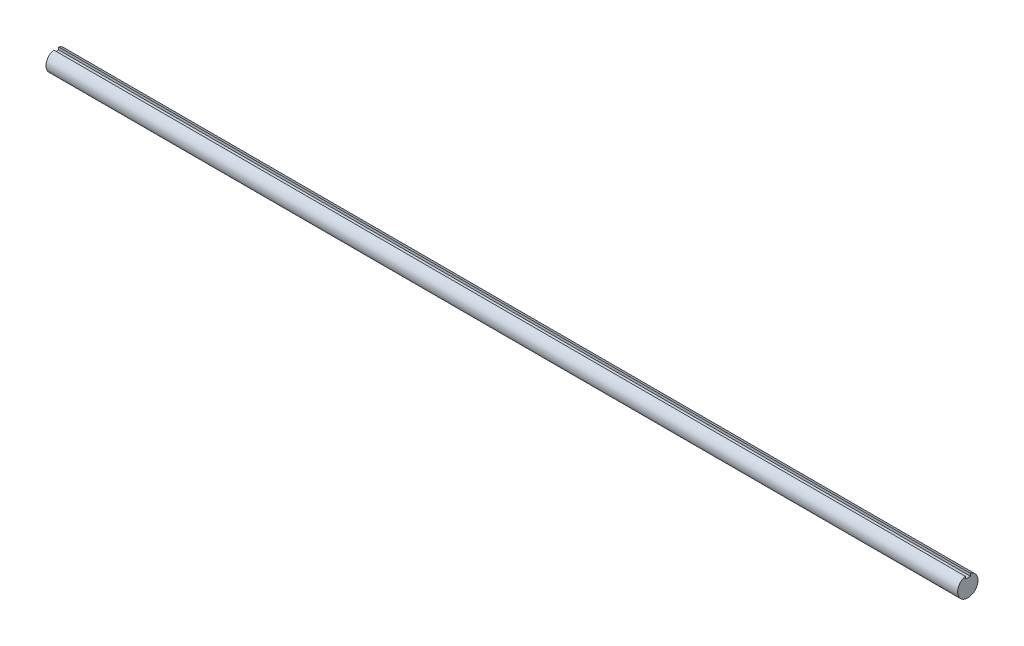
SolidWorks part; units mm, degrees
material "AISI 1020 Steel, Cold Rolled"
ref_plane "Front Plane" through (0, 0, 0) normal (0, 0, 1) x (1, 0, 0)
ref_plane "Top Plane" through (0, 0, 0) normal (0, 1, 0) x (1, 0, 0)
ref_plane "Right Plane" through (0, 0, 0) normal (1, 0, 0) x (0, 0, -1)
sketch "Sketch1" plane through (0, 0, 0) normal (1, 0, 0) x (0, 0, -1)
  line L1 (-1.5875, 6.1484) -> (1.5875, 6.1484) construction
  line L2 (-1.5875, 6.1484) -> (-1.5875, 4.5609)
  line L3 (-1.5875, 4.5609) -> (1.5875, 4.5609)
  line L4 (1.5875, 6.1484) -> (1.5875, 4.5609)
  arc A0 (-1.5875, 6.1484) -> (1.5875, 6.1484) centre (0, 0) ccw
  point P7 (0, 0)
  dimension "D1" = 12.7
  dimension "D2" = 3.175
  dimension "D3" = 1.5875
extrude "Boss-Extrude1" add sketch "Sketch1" along normal mid plane 568.325
